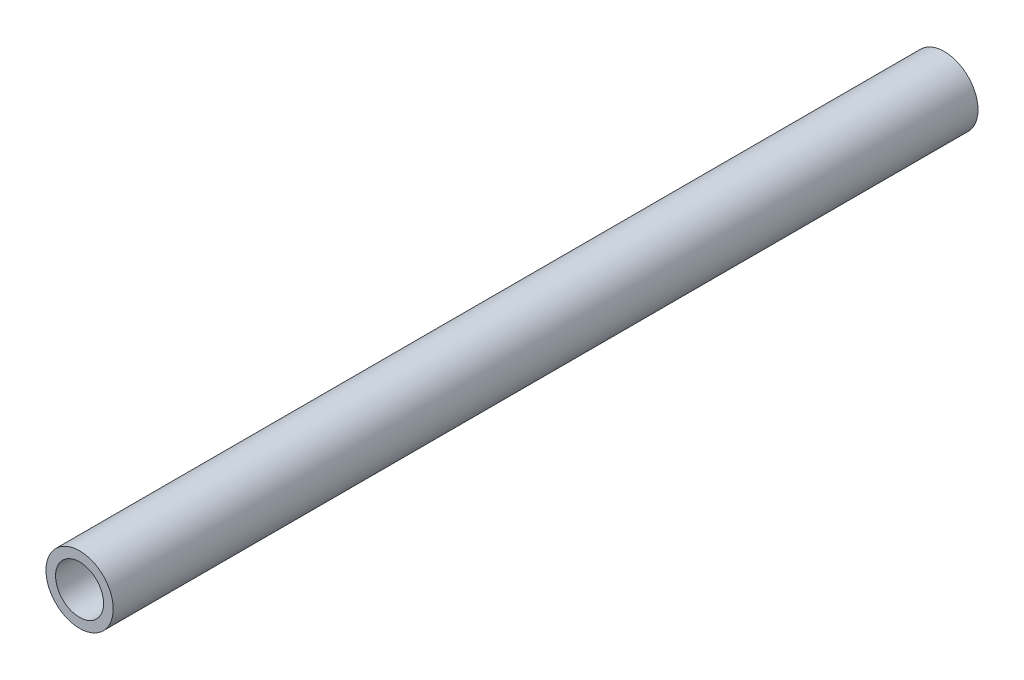
SolidWorks part; units mm, degrees
ref_plane "Front Plane" through (0, 0, 0) normal (0, 0, 1) x (1, 0, 0)
ref_plane "Top Plane" through (0, 0, 0) normal (0, 1, 0) x (1, 0, 0)
ref_plane "Right Plane" through (0, 0, 0) normal (1, 0, 0) x (0, 0, -1)
sketch "Sketch1" plane through (0, 0, 0) normal (0, 0, 1) x (1, 0, 0)
  circle A0 centre (0, 0) radius 3.5
  circle A1 centre (0, 0) radius 2.5
  dimension "D1" = 7
  dimension "D2" = 5
extrude "Boss-Extrude1" add sketch "Sketch1" along normal blind 90
